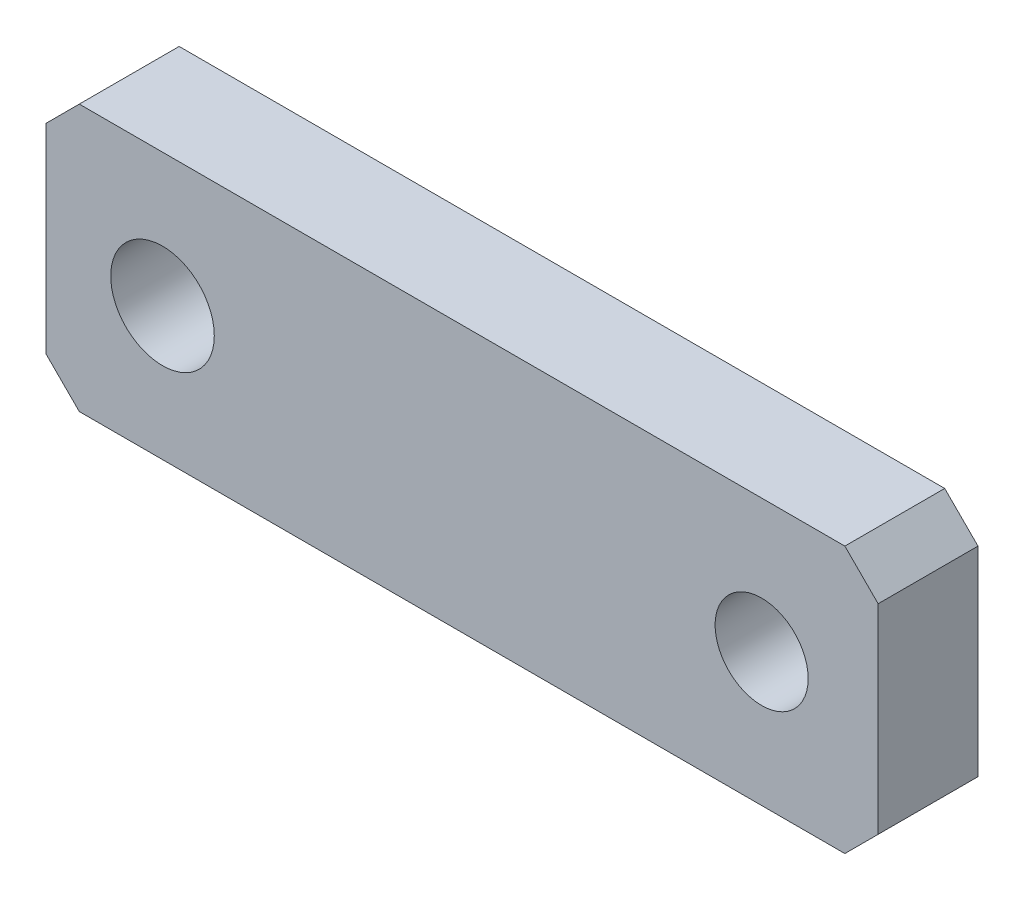
SolidWorks part; units mm, degrees
ref_plane "Front Plane" through (0, 0, 0) normal (0, 0, 1) x (1, 0, 0)
ref_plane "Top Plane" through (0, 0, 0) normal (0, 1, 0) x (1, 0, 0)
ref_plane "Right Plane" through (0, 0, 0) normal (1, 0, 0) x (0, 0, -1)
sketch "Sketch1" plane through (0, 0, 0) normal (0, 0, 1) x (1, 0, 0)
  line L1 (-25, 8) -> (25, 8)
  line L2 (-25, 8) -> (-25, -8)
  line L3 (-25, -8) -> (25, -8)
  line L4 (25, 8) -> (25, -8)
  line L5 (-25, 8) -> (25, -8) construction
  line L6 (-25, -8) -> (25, 8) construction
  circle A0 centre (-18, 0) radius 3.1124
  circle A1 centre (18, 0) radius 2.7952
  point P0 (0, 0)
  point P10 (0, 0)
  dimension "D4" = 36
  dimension "D1" = 50
  dimension "D2" = 16
  dimension "D3" = 7
extrude "Boss-Extrude1" add sketch "Sketch1" along normal blind 6
chamfer "Chamfer1" distance 2 angle 45 4 edges at (-25, -8, 3) (25, -8, 3) (25, 8, 3) (-25, 8, 3)
